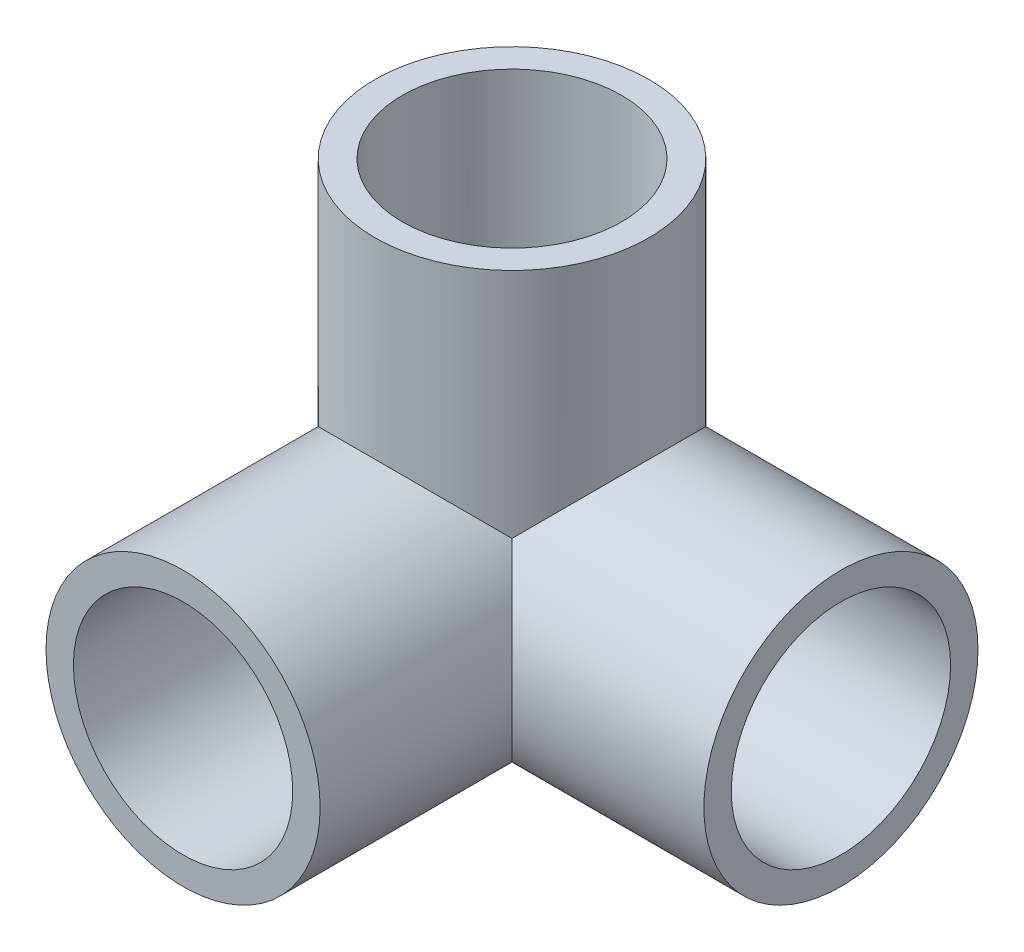
SolidWorks part; units mm, degrees
material "PVC Rigid"
ref_plane "Front Plane" through (0, 0, 0) normal (0, 0, 1) x (1, 0, 0)
ref_plane "Top Plane" through (0, 0, 0) normal (0, 1, 0) x (1, 0, 0)
ref_plane "Right Plane" through (0, 0, 0) normal (1, 0, 0) x (0, 0, -1)
sketch "Sketch1" plane through (0, 0, 0) normal (0, 0, 1) x (1, 0, 0)
  circle A0 centre (0, 0) radius 12.7
  circle A1 centre (0, 0) radius 15.875
  dimension "D1" = 31.75
  dimension "D2" = 25.4
extrude "Boss-Extrude1" add sketch "Sketch1" along normal blind 38.1
sketch "Sketch2" plane through (0, 0, 0) normal (0, 1, 0) x (1, 0, 0)
  line L0 (15.875, 0) -> (-15.875, 0) construction
  line L1 (15.875, 0) -> (-15.875, 0)
  circle A0 centre (0, 0) radius 12.7
  circle A1 centre (0, 0) radius 15.875
  dimension "D1" = 25.4
extrude "Boss-Extrude2" add sketch "Sketch2" along normal blind 38.1 contours L1 A1 A0 | L1 A1 A0
sketch "Sketch3" plane through (0, 0, 0) normal (1, 0, 0) x (0, 0, -1)
  circle A0 centre (0, 0) radius 15.875
  circle A1 centre (0, 0) radius 12.7
  dimension "D1" = 25.4
extrude "Boss-Extrude3" add sketch "Sketch3" along normal blind 38.1
sketch "Sketch4" plane through (0, 0, 0) normal (-1, 0, 0) x (0, 0, 1)
  line L2 (0, -15.875) -> (0, -12.7)
  line L3 (-12.7, 0) -> (-15.875, 0)
  line L4 (0, -15.875) -> (0, -12.7)
  line L5 (-12.7, 0) -> (-15.875, 0)
  arc A2 (-15.875, 0) -> (0, -15.875) centre (0, 0) ccw
  arc A3 (-12.7, 0) -> (0, -12.7) centre (0, 0) ccw
  arc A4 (-15.875, 0) -> (0, -15.875) centre (0, 0) ccw
  arc A5 (-12.7, 0) -> (0, -12.7) centre (0, 0) ccw
  dimension "D1" = 0
revolve "Revolve1" add sketch "Sketch4" angle 90 about L5
sketch "Sketch5" plane through (0, 38.1, 0) normal (0, 1, 0) x (1, 0, 0)
  circle A0 centre (0, 0) radius 12.7 construction
  circle A1 centre (0, 0) radius 12.7
extrude "Cut-Extrude1" cut sketch "Sketch5" against normal up to vertex (38.1 mm away)
sketch "Sketch6" plane through (0, 0, 38.1) normal (0, 0, 1) x (1, 0, 0)
  circle A0 centre (0, 0) radius 12.7 construction
  circle A1 centre (0, 0) radius 12.7
extrude "Cut-Extrude2" cut sketch "Sketch6" against normal up to vertex (38.1 mm away) up to point (0, -12.7, 0)
sketch "Sketch7" plane through (38.1, 0, 0) normal (1, 0, 0) x (0, 0, -1)
  circle A0 centre (0, 0) radius 12.7 construction
  circle A1 centre (0, 0) radius 12.7
extrude "Cut-Extrude3" cut sketch "Sketch7" against normal up to vertex
move or copy body "Body-Move/Copy1" [suppressed] bodies to move or copy 104
